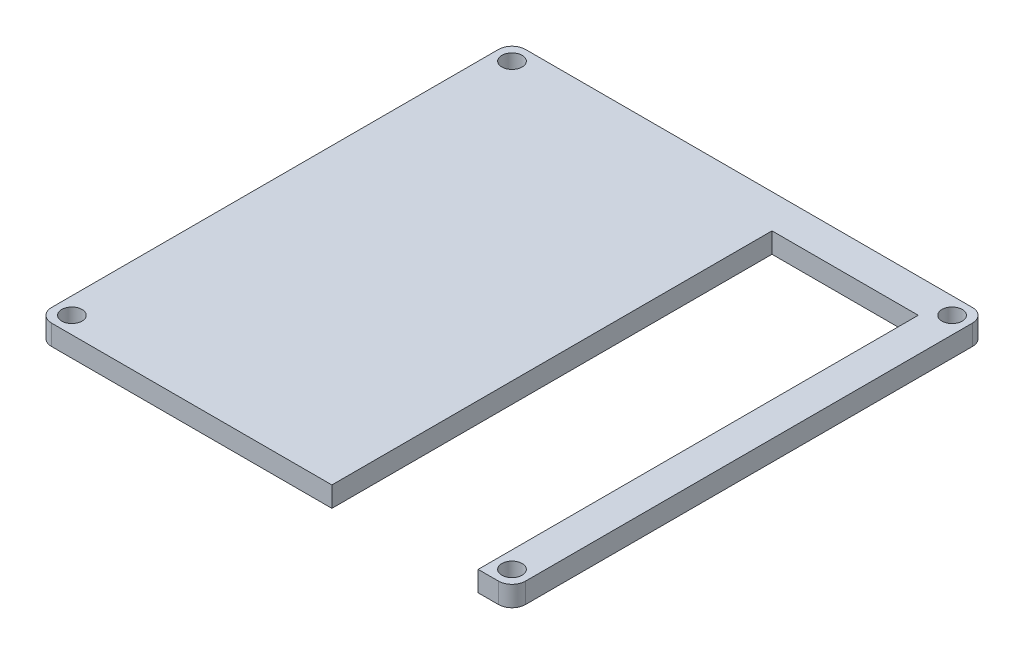
SolidWorks part; units mm, degrees
ref_plane "Front Plane" through (0, 0, 0) normal (0, 0, 1) x (1, 0, 0)
ref_plane "Top Plane" through (0, 0, 0) normal (0, 1, 0) x (1, 0, 0)
ref_plane "Right Plane" through (0, 0, 0) normal (1, 0, 0) x (0, 0, -1)
sketch "Sketch1" plane through (0, 0, 0) normal (0, 1, 0) x (1, 0, 0)
  line L1 (-35, 35) -> (35, 35)
  line L2 (-35, 35) -> (-35, -35)
  line L3 (-35, -35) -> (35, -35)
  line L4 (35, 35) -> (35, -35)
  line L5 (-35, 35) -> (35, -35) construction
  line L6 (-35, -35) -> (35, 35) construction
  circle A0 centre (-32.5, 32.5) radius 1.5
  circle A1 centre (32.5, 32.5) radius 1.5
  circle A2 centre (32.5, -32.5) radius 1.5
  circle A3 centre (-32.5, -32.5) radius 1.5
  point P0 (0, 0)
  dimension "D4" = 3
  dimension "D1" = 70
  dimension "D2" = 70
  dimension "D3" = 2.5
  dimension "D5" = 2
extrude "Boss-Extrude1" add sketch "Sketch1" along normal blind 3
fillet "Fillet1" radius 2 4 edges at (-35, 1.5, -35) (35, 1.5, -35) (35, 1.5, 35) (-35, 1.5, 35)
sketch "Sketch2" plane through (0, 3, 0) normal (0, 1, 0) x (1, 0, 0)
  line L0 (35, -33) -> (35, 33) construction
  line L1 (8.4, -40) -> (30, -40)
  line L2 (8.4, -40) -> (8.4, 30)
  line L3 (8.4, 30) -> (30, 30)
  line L4 (30, -40) -> (30, 30)
  line L5 (8.4, -40) -> (30, 30) construction
  line L6 (8.4, 30) -> (30, -40) construction
  line L7 (33, 35) -> (-33, 35) construction
  point P0 (19.2, -5)
  dimension "D1" = 21.6
  dimension "D2" = 5
  dimension "D3" = 70
  dimension "D4" = 40
extrude "Cut-Extrude2" cut sketch "Sketch2" against normal blind 10
